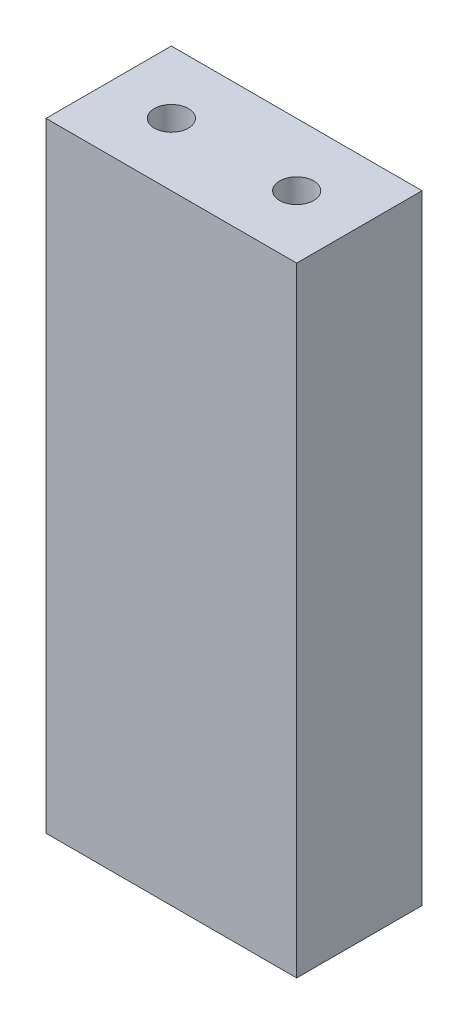
SolidWorks part; units mm, degrees
ref_plane "Front Plane" through (0, 0, 0) normal (0, 0, 1) x (1, 0, 0)
ref_plane "Top Plane" through (0, 0, 0) normal (0, 1, 0) x (1, 0, 0)
ref_plane "Right Plane" through (0, 0, 0) normal (1, 0, 0) x (0, 0, -1)
sketch "Sketch1" plane through (0, 0, 0) normal (0, 1, 0) x (1, 0, 0)
  line L1 (0, 0) -> (25.4, 0)
  line L2 (0, 0) -> (0, -12.7)
  line L3 (0, -12.7) -> (25.4, -12.7)
  line L4 (25.4, 0) -> (25.4, -12.7)
  dimension "D1" = 12.7
  dimension "D2" = 25.4
extrude "Boss-Extrude1" add sketch "Sketch1" along normal blind 62.738
sketch "Sketch3" plane through (0, 0, 0) normal (0, -1, 0) x (1, 0, 0)
  line L0 (25.4, 12.7) -> (25.4, 0) construction
  point P3 (25.4, 6.35)
  point P10 (3.175, 6.35)
  point P11 (22.225, 6.35)
sketch "Sketch4" plane through (0, 62.738, 0) normal (0, 1, 0) x (1, 0, 0)
  line L0 (0, 0) -> (0, -12.7) construction
  circle A0 centre (6.35, -6.35) radius 2.1982
  circle A1 centre (19.05, -6.35) radius 2.1047
  point P0 (6.35, -6.35)
  point P1 (19.05, -6.35)
  point P8 (0, -6.35)
  dimension "D1" = 12.7
  dimension "D2" = 6.35
hole_wizard "#2-56 Tapped Hole1" positions "Sketch11" profile "Sketch12" tap size "#2-56" standard "ANSI Inch"
sketch "Sketch11" plane through (0, 0, 0) normal (0, -1, 0) x (-1, 0, 0)
  point P0 (-3.175, -6.35)
  point P3 (-22.225, -6.35)
sketch "Sketch12" plane through (3.175, 0, 6.35) normal (1, 0, 0) x (0, 0, -1)
  line L0 (0, 0) -> (0, 11.3546)
  line L1 (0, 11.3546) -> (0.889, 10.8204)
  line L2 (0.889, 10.8204) -> (0.889, 0)
  line L5 (0.889, 0) -> (0, 0)
  line L10 (0, 11.3546) -> (-0.889, 10.8204) construction
  line L11 (0, -6.35) -> (0, 107.95) construction
  dimension "Tap Drill Dia." = 1.778
  dimension "Tap Drill Depth" = 10.8204
  dimension "Drill Angle" = 118
hole_wizard "#8-32 Tapped Hole1" positions "Sketch13" profile "Sketch14" tap size "#8-32" standard "ANSI Inch"
sketch "Sketch13" plane through (0, 62.738, 0) normal (0, 1, 0) x (1, 0, 0)
  point P0 (6.35, -6.35)
  point P3 (19.05, -6.35)
sketch "Sketch14" plane through (6.35, 62.738, 6.35) normal (1, 0, 0) x (0, 0, 1)
  line L0 (0, 0) -> (0, 11.7464)
  line L1 (0, 11.7464) -> (1.7272, 10.7086)
  line L2 (1.7272, 10.7086) -> (1.7272, 0)
  line L5 (1.7272, 0) -> (0, 0)
  line L10 (0, 11.7464) -> (-1.7272, 10.7086) construction
  line L11 (0, -6.35) -> (0, 107.95) construction
  dimension "Tap Drill Dia." = 3.4544
  dimension "Tap Drill Depth" = 10.7086
  dimension "Drill Angle" = 118
cosmetic thread "Hole Thread3" parameters "D1"=8.3312, "D2"=4.1656
cosmetic thread "Hole Thread4" parameters "D1"=8.3312, "D2"=4.1656
